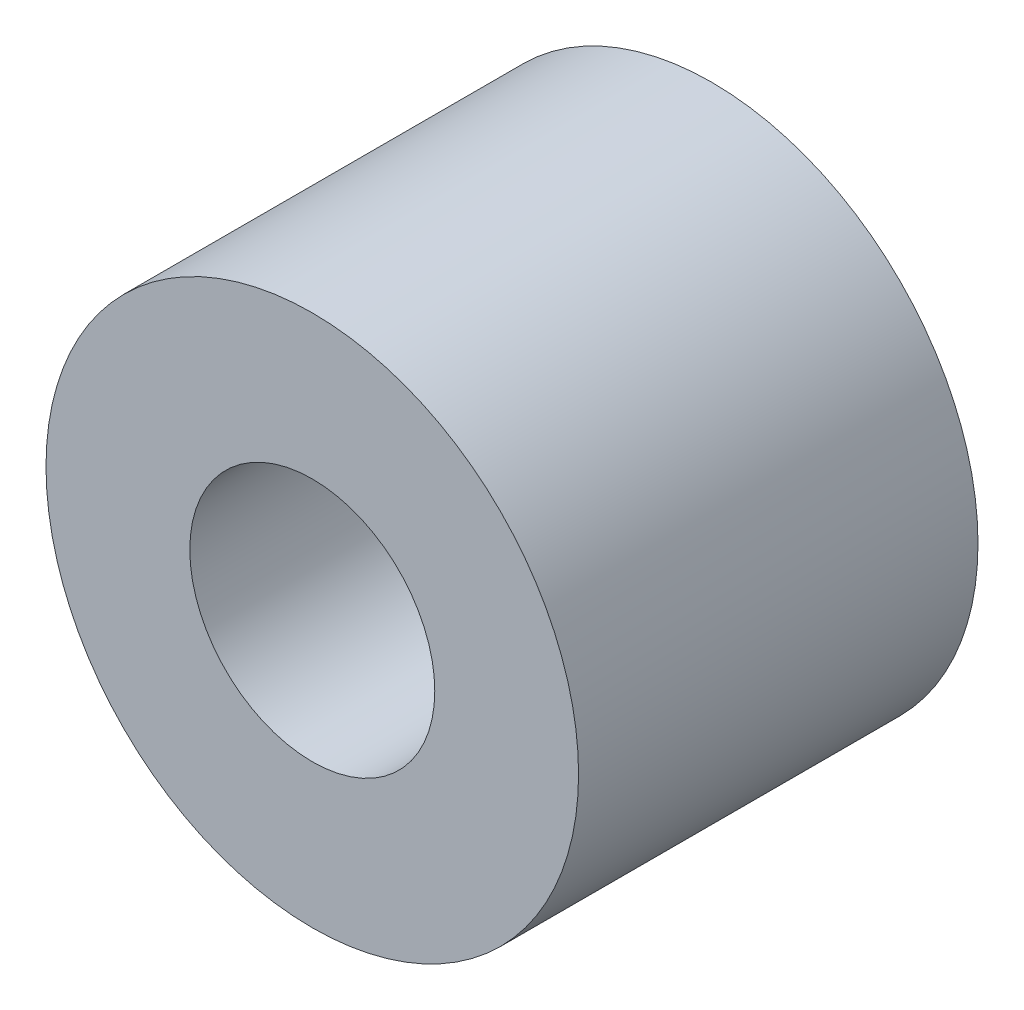
SolidWorks part; units mm, degrees
material "2014-O"
ref_plane "Front Plane" through (0, 0, 0) normal (0, 0, 1) x (1, 0, 0)
ref_plane "Top Plane" through (0, 0, 0) normal (0, 1, 0) x (1, 0, 0)
ref_plane "Right Plane" through (0, 0, 0) normal (1, 0, 0) x (0, 0, -1)
sketch "Sketch1" plane through (0, 0, 0) normal (0, 0, 1) x (1, 0, 0)
  circle A0 centre (0, 0) radius 3.175
  circle A1 centre (0, 0) radius 1.4605
  dimension "OD" = 6.35
  dimension "ID" = 2.921
extrude "Extrude1" add sketch "Sketch1" along normal mid plane 4.7625
sketch "Sketch2" plane through (0, 0, 0) normal (1, 0, 0) x (0, 0, -1)
  line L0 (-2.3813, -1.4605) -> (2.3812, -1.4605) construction
  line L3 (2.3812, 1.4605) -> (-2.3813, 1.4605) construction
  line L5 (-2.3813, -1.4605) -> (2.3812, -1.4605)
  line L6 (2.3812, 1.4605) -> (-2.3813, 1.4605)
sketch "Sketch4" plane through (0, 0, 2.3813) normal (0, 0, 1) x (1, 0, 0)
  line L0 (0, 0) -> (-1.0327, 1.0327)
  line L1 (0, -55) -> (0, 55) construction
  circle A0 centre (0, 0) radius 1.4605 construction
  dimension "D1" = 45
